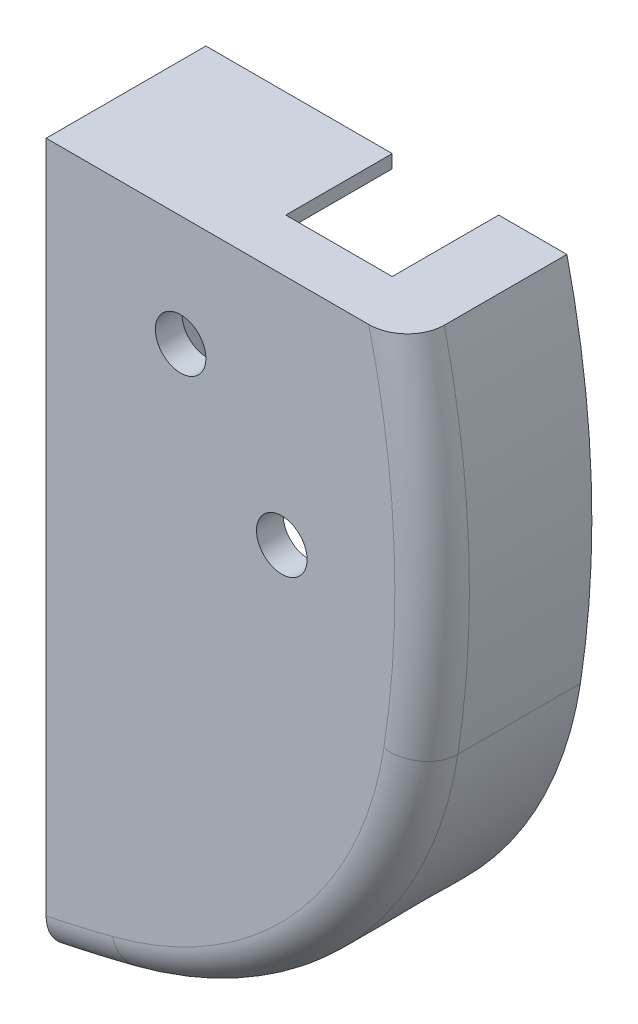
SolidWorks part; units mm, degrees
ref_plane "Front Plane" through (0, 0, 0) normal (0, 0, 1) x (1, 0, 0)
ref_plane "Top Plane" through (0, 0, 0) normal (0, 1, 0) x (1, 0, 0)
ref_plane "Right Plane" through (0, 0, 0) normal (1, 0, 0) x (0, 0, -1)
sketch "Sketch1" plane through (0, 0, 0) normal (0, 0, 1) x (1, 0, 0)
  line L0 (0, 0) -> (67.8, 0)
  line L1 (55, 0) -> (-55, 0) construction
  line L2 (67.8, 0) -> (-107.2, -40.8) construction
  line L3 (70.3411, -68.5271) -> (-4.7487, -56.8001) construction
  line L4 (14.2335, -130.3914) -> (-53.6029, 132.6006) construction
  line L5 (0, 0) -> (0, -133.6573)
  arc A0 (67.8, 0) -> (70.3411, -68.5271) centre (-107.2, -40.8) cw
  arc A1 (70.3411, -68.5271) -> (14.2335, -130.3914) centre (-4.7487, -56.8001) cw
  arc A2 (14.2335, -130.3914) -> (0, -133.6573) centre (-53.6029, 132.6006) cw
  dimension "D4" = 271.6
  dimension "D6" = 22
  dimension "D1" = 67.8
  dimension "D2" = 175
  dimension "D3" = 40.8
  dimension "D5" = 76
extrude "Boss-Extrude1" add sketch "Sketch1" along normal blind 30
sketch "Sketch4" plane through (0, 0, 0) normal (0, 0, -1) x (-1, 0, 0)
  line L8 (-35, -10) -> (-28.3043, 16.5084) construction
  line L16 (-10, -121.1497) -> (-10, -10)
  line L17 (-10, -10) -> (-59.6746, -10)
  line L18 (-10, -121.1497) -> (-10, -10)
  line L19 (-10, -10) -> (-59.6746, -10)
  arc A20 (-59.6746, -10) -> (-60.4609, -66.984) centre (107.2, -40.8) ccw
  arc A21 (-60.4609, -66.984) -> (-11.7359, -120.7083) centre (4.7487, -56.8001) ccw
  arc A22 (-11.7359, -120.7083) -> (-10, -121.1497) centre (53.6029, 132.6006) ccw
  arc A23 (-59.6746, -10) -> (-60.4609, -66.984) centre (107.2, -40.8) ccw
  arc A24 (-60.4609, -66.984) -> (-11.7359, -120.7083) centre (4.7487, -56.8001) ccw
  arc A25 (-11.7359, -120.7083) -> (-10, -121.1497) centre (53.6029, 132.6006) ccw
  dimension "D1" = 10
extrude "Cut-Extrude2" cut sketch "Sketch4" against normal blind 20
fillet "Fillet1" radius 7 3 edges at (7.1387, -132.12, 30) (51.5468, -107.8571, 30) (72.3698, -34.1412, 30)
sketch "Sketch9" plane through (0, -10, 0) normal (0, -1, 0) x (1, 0, 0)
  line L7 (10, 20) -> (59.6746, 20) construction
  line L9 (55, 20) -> (35, 20)
  line L10 (35, 20) -> (35, 0)
  line L11 (10, 0) -> (59.6746, 0) construction
  line L12 (35, 0) -> (55, 0)
  line L13 (55, 0) -> (55, 20)
extrude "Cut-Extrude7" cut sketch "Sketch9" against normal through all
sketch "Sketch10" plane through (0, 0, 20) normal (0, 0, -1) x (-1, 0, 0)
  line L3 (-44.2597, -44.037) -> (-25.2558, -20.8238) construction
  circle A0 centre (-44.2597, -44.037) radius 4.75
  circle A1 centre (-25.2558, -20.8238) radius 4.75
extrude "Cut-Extrude8" cut sketch "Sketch10" against normal blind 10
sketch "Sketch12" plane through (0, 0, 0) normal (0, 0, -1) x (-1, 0, 0)
  line L0 (-38.1592, -106.949) -> (-38.2609, -106.8618) construction
  line L1 (-38.2609, -106.8618) -> (-23.9631, -119.0951) construction
  line L2 (-23.9631, -119.0951) -> (-23.6772, -118.761) construction
  line L3 (-23.6772, -118.761) -> (-25.2634, -120.6148) construction
  line L4 (-25.2634, -120.6148) -> (-49.8594, -99.5702) construction
  line L5 (-49.8594, -99.5702) -> (-48.5591, -98.0505) construction
  line L6 (-48.5591, -98.0505) -> (-38.2609, -106.8618) construction
  line L7 (-38.1592, -106.949) -> (-44.6604, -114.5473) construction
  line L8 (-44.6604, -114.5473) -> (-26.4379, -130.1387) construction
  line L9 (-38.1592, -106.949) -> (-39.4594, -108.4685) construction
  line L10 (-47.0577, -101.9673) -> (-31.8611, -114.9697)
  line L11 (-31.8611, -114.9697) -> (-28.2162, -110.7098)
  line L12 (-28.2162, -110.7098) -> (-43.4129, -97.7074)
  line L13 (-47.0577, -101.9673) -> (-43.4129, -97.7074)
  arc A0 (-60.4609, -66.984) -> (-11.7359, -120.7083) centre (4.7487, -56.8001) ccw construction
  arc A1 (-70.3411, -68.5271) -> (-14.2335, -130.3914) centre (4.7487, -56.8001) ccw construction
  point P21 (-35.8145, -104.2086)
  dimension "D1" = 360
  dimension "D2" = 2
  dimension "D3" = 8.0001
extrude "Cut-Extrude9" cut sketch "Sketch12" against normal blind 20
sketch "Sketch13" plane through (70.2592, -82.1159, 0) normal (-0.6501, 0.7598, 0) x (0.7598, 0.6501, 0)
  line L0 (-40.5351, 0) -> (-40.5351, -20) construction
  line L1 (-30.5351, 0) -> (-50.5351, 0) construction
  line L2 (-30.5351, -20) -> (-50.5351, -20) construction
  circle A0 centre (-40.5351, -10) radius 6
extrude "Cut-Extrude10" cut sketch "Sketch13" against normal blind 20
ref_plane "Plane1" through (75.4602, -88.1945, 0) normal (-0.6501, 0.7598, 0) x (0.7598, 0.6501, 0)
sketch "Sketch14" plane through (75.4602, -88.1945, 0) normal (-0.6501, 0.7598, 0) x (0.7598, 0.6501, 0)
  line L0 (-40.5351, -10) -> (-40.8375, -22.1955) construction
  circle A0 centre (-40.5351, -10) radius 9
extrude "Cut-Extrude11" cut sketch "Sketch14" along normal blind 4
sketch "Sketch15" plane through (0, 0, 20) normal (0, 0, -1) x (-1, 0, 0)
  line L0 (-33.5875, -37.5289) -> (-22.5213, -55.6756)
  line L1 (-22.5213, -55.6756) -> (-43.8656, -68.6918)
  line L2 (-43.8656, -68.6918) -> (-54.9318, -50.5451)
  line L3 (-30.7698, -32.0419) -> (-45.8791, -24.6153)
  line L4 (-45.8791, -24.6153) -> (-34.8512, -2.1791)
  line L5 (-34.8512, -2.1791) -> (-21.0171, -9.0644)
  arc A0 (-33.5875, -37.5289) -> (-54.9318, -50.5451) centre (-44.2597, -44.037) ccw
  arc A1 (-30.7698, -32.0419) -> (-21.0171, -9.0644) centre (-25.2558, -20.8238) ccw
  dimension "D1" = 25
  dimension "D2" = 25
extrude "Cut-Extrude12" cut sketch "Sketch15" against normal blind 5
sketch "Sketch16" plane through (0, 0, 25) normal (0, 0, -1) x (-1, 0, 0)
  line L0 (-21.0171, -9.0644) -> (-34.8512, -2.1791)
  line L1 (-34.8512, -2.1791) -> (-38.2355, -9.0644)
  line L2 (-34.8512, -2.1791) -> (-45.8791, -24.6153) construction
  line L3 (-38.2355, -9.0644) -> (-15.3389, -20.3187)
  line L4 (-15.3389, -20.3187) -> (-14.3644, -26.958)
  arc A0 (-14.3644, -26.958) -> (-21.0171, -9.0644) centre (-25.2558, -20.8238) ccw
  arc A1 (-30.7698, -32.0419) -> (-21.0171, -9.0644) centre (-25.2558, -20.8238) ccw construction
extrude "Cut-Extrude13" cut sketch "Sketch16" along normal blind 30
sketch "Sketch17" plane through (0, 0, 0) normal (-1, 0, 0) x (0, 0, 1)
  line L0 (0, -133.6573) -> (10, -133.6573) construction
  line L1 (0, 0) -> (0, -133.6573) construction
  line L2 (23, -133.6573) -> (0, -133.6573) construction
  line L3 (10, -133.6573) -> (10, -73.6573) construction
  line L4 (10, -73.6573) -> (10, -23.6573) construction
  circle A0 centre (10, -73.6573) radius 3
  circle A1 centre (10, -23.6573) radius 3
  dimension "D1" = 60
  dimension "D2" = 50
extrude "Cut-Extrude14" cut sketch "Sketch17" against normal blind 10
sketch "Sketch18" plane through (0, 0, 0) normal (-1, 0, 0) x (0, 0, 1)
  line L0 (10, -73.6573) -> (10, -83.6573) construction
  line L1 (10, -83.6573) -> (2.5, -83.6573) construction
  line L2 (10, -23.6573) -> (10, -13.6573) construction
  line L3 (10, -13.6573) -> (17.5, -13.6573) construction
  line L4 (10, -83.6573) -> (2.5, -83.6573)
  line L5 (2.5, -83.6573) -> (2.5, -13.6573)
  line L6 (2.5, -13.6573) -> (17.5, -13.6573)
  line L7 (17.5, -13.6573) -> (17.5, -83.6573)
  line L8 (17.5, -83.6573) -> (10, -83.6573)
  circle A0 centre (10, -73.6573) radius 3
  circle A1 centre (10, -23.6573) radius 3
extrude "Boss-Extrude2" add sketch "Sketch18" along normal blind 2.5
chamfer "Chamfer1" distance 1 angle 45 10 edges at (-2.5, -26.6573, 10) (-2.5, -76.6573, 10) (-2.5, -48.6573, 2.5) (-1.25, -13.6573, 2.5) (-2.5, -13.6573, 10) (-1.25, -13.6573, 17.5) (-2.5, -48.6573, 17.5) (-1.25, -83.6573, 17.5) (-2.5, -83.6573, 10) (-1.25, -83.6573, 2.5)
sketch "Sketch19" plane through (0, 0, 0) normal (0, 0, -1) x (-1, 0, 0)
  line L0 (0, -133.6573) -> (0, -123.6573) construction
  line L1 (0, -123.6573) -> (-2, -123.6573) construction
  line L2 (-2, -123.6573) -> (-8, -123.6573)
  line L3 (-8, -123.6573) -> (-8, -107.6573)
  line L4 (-8, -107.6573) -> (-2, -107.6573)
  line L5 (-2, -107.6573) -> (-2, -123.6573)
  arc A0 (-14.2335, -130.3914) -> (0, -133.6573) centre (53.6029, 132.6006) ccw construction
  dimension "D1" = 2
  dimension "D2" = 6
extrude "Cut-Extrude15" cut sketch "Sketch19" against normal blind 6
sketch "Sketch20" plane through (0, 0, 0) normal (0, 0, -1) x (-1, 0, 0)
  line L0 (-70.3411, -68.5271) -> (-52.3411, -68.5271) construction
  line L1 (-52.3411, -68.5271) -> (-52.3411, -78.5271) construction
  circle A0 centre (-52.3411, -78.5271) radius 14
  dimension "D1" = 18
  dimension "D2" = 10
extrude "Boss-Extrude3" add sketch "Sketch20" against normal blind 16
sketch "Sketch21" plane through (0, 0, 0) normal (0, 0, -1) x (-1, 0, 0)
  line L0 (-49.17, -64.8909) -> (-52.3411, -78.5271) construction
  arc A0 (-50.8, -92.442) -> (-60.4413, -67.1084) centre (-52.3411, -78.5271) ccw construction
  circle A1 centre (-52.3411, -78.5271) radius 12.5
extrude "Cut-Extrude16" cut sketch "Sketch21" against normal blind 6 contours A1
sketch "Sketch22" plane through (0, 0, 6) normal (0, 0, -1) x (-1, 0, 0)
  line L0 (-64.2948, -74.8718) -> (-52.3411, -78.5271) construction
  circle A0 centre (-52.3411, -78.5271) radius 12.5 construction
  circle A1 centre (-52.3411, -78.5271) radius 10.5
extrude "Cut-Extrude17" cut sketch "Sketch22" against normal blind 6
